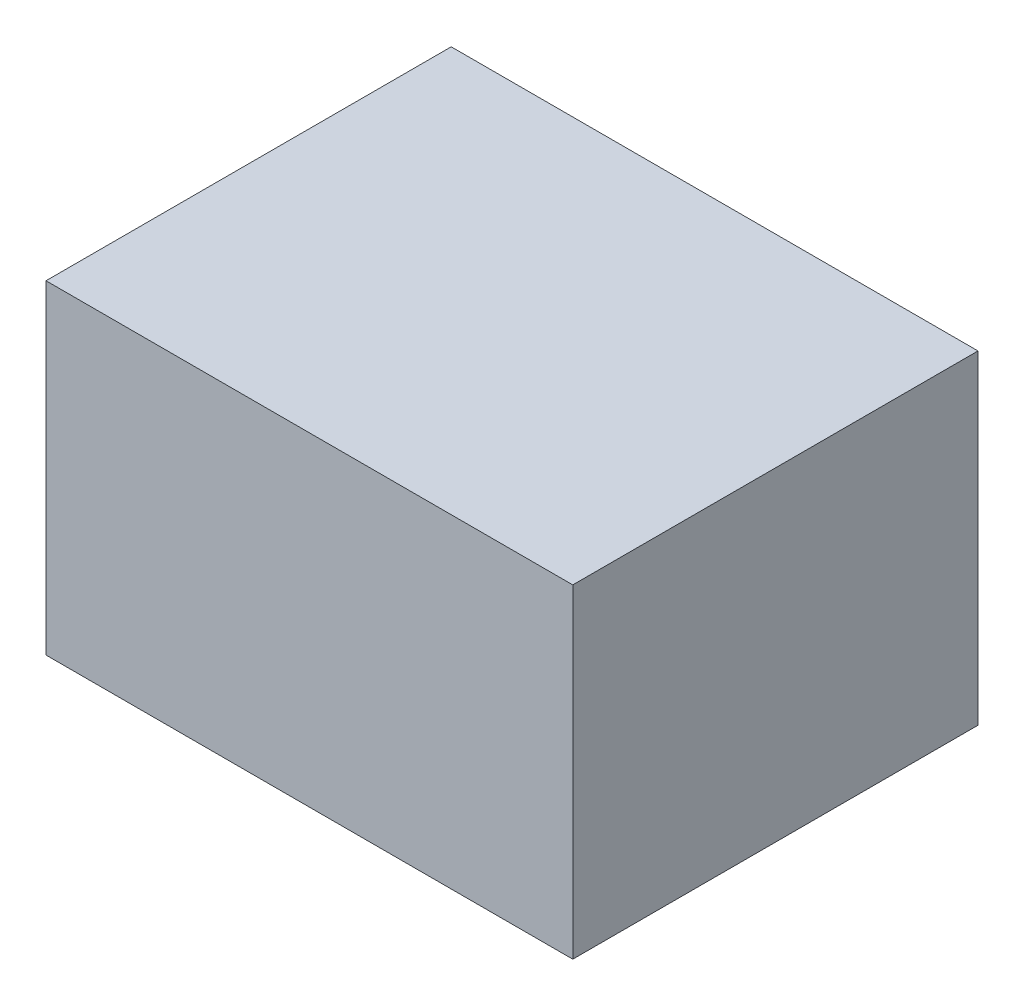
SolidWorks part; units mm, degrees
ref_plane "Plan de face" through (0, 0, 0) normal (0, 0, 1) x (1, 0, 0)
ref_plane "Plan de dessus" through (0, 0, 0) normal (0, 1, 0) x (1, 0, 0)
ref_plane "Plan de droite" through (0, 0, 0) normal (1, 0, 0) x (0, 0, -1)
sketch "Esquisse1" plane through (0, 0, 0) normal (0, 0, 1) x (1, 0, 0)
  line L1 (0, 0) -> (65, 0)
  line L2 (0, 0) -> (0, -40)
  line L3 (0, -40) -> (65, -40)
  line L4 (65, 0) -> (65, -40)
  dimension "D1" = 65
  dimension "D2" = 40
extrude "Boss.-Extru.1" add sketch "Esquisse1" along normal blind 50
